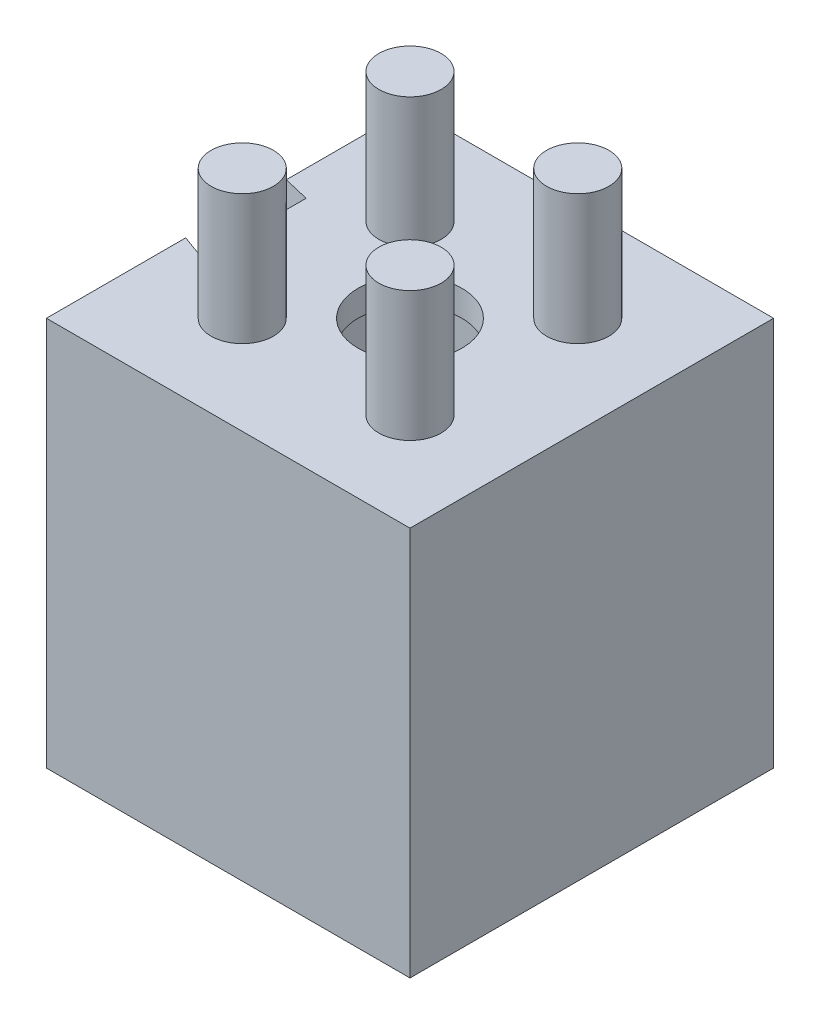
SolidWorks part; units mm, degrees
ref_plane "Front Plane" through (0, 0, 0) normal (0, 0, 1) x (1, 0, 0)
ref_plane "Top Plane" through (0, 0, 0) normal (0, 1, 0) x (1, 0, 0)
ref_plane "Right Plane" through (0, 0, 0) normal (1, 0, 0) x (0, 0, -1)
sketch "Sketch1" plane through (0, 0, 0) normal (0, 1, 0) x (1, 0, 0)
  line L0 (-11.899, 8.5638) -> (-11.899, -3.4362)
  line L1 (-11.899, -3.4362) -> (0.101, -3.4362)
  line L2 (0.101, -3.4362) -> (0.101, 8.5638)
  line L3 (0.101, 8.5638) -> (-11.899, 8.5638)
  line L4 (-11.899, 8.5638) -> (0.101, -3.4362) construction
  line L5 (-11.899, -3.4362) -> (0.101, 8.5638) construction
  line L7 (-12.399, -3.9362) -> (0.601, -3.9362)
  line L8 (0.601, -3.9362) -> (0.601, 9.0638)
  line L9 (0.601, 9.0638) -> (-12.399, 9.0638)
  line L10 (-5.899, 8.5638) -> (-5.899, -3.4362) construction
  line L11 (-11.899, 2.5638) -> (0.101, 2.5638) construction
  line L12 (-12.399, 9.0638) -> (-12.399, 5.0638)
  line L13 (-12.399, 9.0638) -> (-12.399, -3.9362) construction
  line L14 (-12.399, 5.0638) -> (-11.899, 5.0638)
  line L15 (-12.399, -3.9362) -> (-12.399, 0.0638)
  line L16 (-12.399, 0.0638) -> (-11.899, 0.0638)
  line L17 (-11.899, 5.0638) -> (-11.899, 8.5638)
  line L18 (0.101, 8.5638) -> (0.101, -3.4362)
  line L19 (-11.899, -3.4362) -> (-11.899, 0.0638)
  line L20 (-12.399, 0.0638) -> (-12.399, -3.9362)
  line L21 (0.601, -3.9362) -> (0.601, 9.0638)
  line L22 (-12.399, 9.0638) -> (-12.399, 5.0638)
  line L23 (-11.899, 0.0638) -> (-11.899, -3.4362)
  line L24 (-11.899, 8.5638) -> (-11.899, 5.0638)
  line L25 (-11.899, 8.5638) -> (0.101, 8.5638)
  line L26 (0.101, -3.4362) -> (-11.899, -3.4362)
  circle A0 centre (-5.899, 2.5638) radius 2
  circle A2 centre (-8.2699, 4.9348) radius 0.4
  circle A3 centre (-3.5281, 4.9348) radius 0.4
  circle A4 centre (-3.5281, 0.1929) radius 0.4
  circle A5 centre (-8.2699, 0.1929) radius 0.4
  point P22 (-8.401, 5.2933)
  dimension "D3" = 0.5
  dimension "D4" = 4
  dimension "D1" = 12
  dimension "D2" = 12
  dimension "D5" = 4
extrude "Boss-Extrude2" add sketch "Sketch1" along normal blind 1 contours L3 L0 L1 L2 | A0
sketch "Sketch3" plane through (0, 1, 0) normal (0, 1, 0) x (1, 0, 0)
  line L0 (-12.899, -4.4362) -> (-12.899, 0.9281)
  line L1 (-12.899, 0.9281) -> (-11.899, 0.5638)
  line L2 (-11.899, 4.5638) -> (-11.899, 8.5638)
  line L3 (-11.899, 8.5638) -> (0.101, 8.5638)
  line L4 (-12.899, 9.5638) -> (-12.899, 4.8009)
  line L5 (-12.899, 4.8009) -> (-11.899, 4.5638)
  line L6 (-11.899, 8.5638) -> (-11.899, -3.4362) construction
  line L8 (1.101, -4.4362) -> (1.101, 9.5638)
  line L9 (1.101, 9.5638) -> (-12.899, 9.5638)
  line L10 (-12.899, 9.5638) -> (-12.899, -4.4362)
  line L11 (-12.899, -4.4362) -> (1.101, -4.4362)
  line L12 (1.101, -4.4362) -> (1.101, 9.5638)
  line L13 (1.101, 9.5638) -> (-12.899, 9.5638)
  line L15 (-12.899, -4.4362) -> (1.101, -4.4362)
  line L16 (0.101, 8.5638) -> (0.101, -3.4362)
  line L17 (0.101, -3.4362) -> (-11.899, -3.4362)
  line L18 (-11.899, -3.4362) -> (-11.899, 0.5638)
  dimension "D2" = 4
  dimension "D3" = 4
  dimension "D1" = 1
extrude "Boss-Extrude5" add sketch "Sketch3" against normal blind 15
sketch "Sketch4" plane through (0, 1, 0) normal (0, 1, 0) x (1, 0, 0)
  line L0 (-5.899, 9.5638) -> (-5.899, -4.4362) construction
  line L1 (1.101, 9.5638) -> (-12.899, 9.5638) construction
  line L2 (-12.899, -4.4362) -> (1.101, -4.4362) construction
  line L3 (-11.899, 2.5638) -> (1.101, 2.5638) construction
  line L4 (-11.899, 4.5638) -> (-11.899, 0.5638) construction
  line L5 (1.101, -4.4362) -> (1.101, 9.5638) construction
  line L6 (-12.899, 9.5638) -> (1.101, -4.4362) construction
  circle A1 centre (-9.1287, 5.7935) radius 1.2
  circle A2 centre (-2.6693, 5.7935) radius 1.2
  circle A3 centre (-2.6693, -0.6659) radius 1.2
  circle A4 centre (-9.1287, -0.6659) radius 1.2
  point P24 (-9.008, 5.912)
extrude "Boss-Extrude6" add sketch "Sketch4" along normal blind 5
